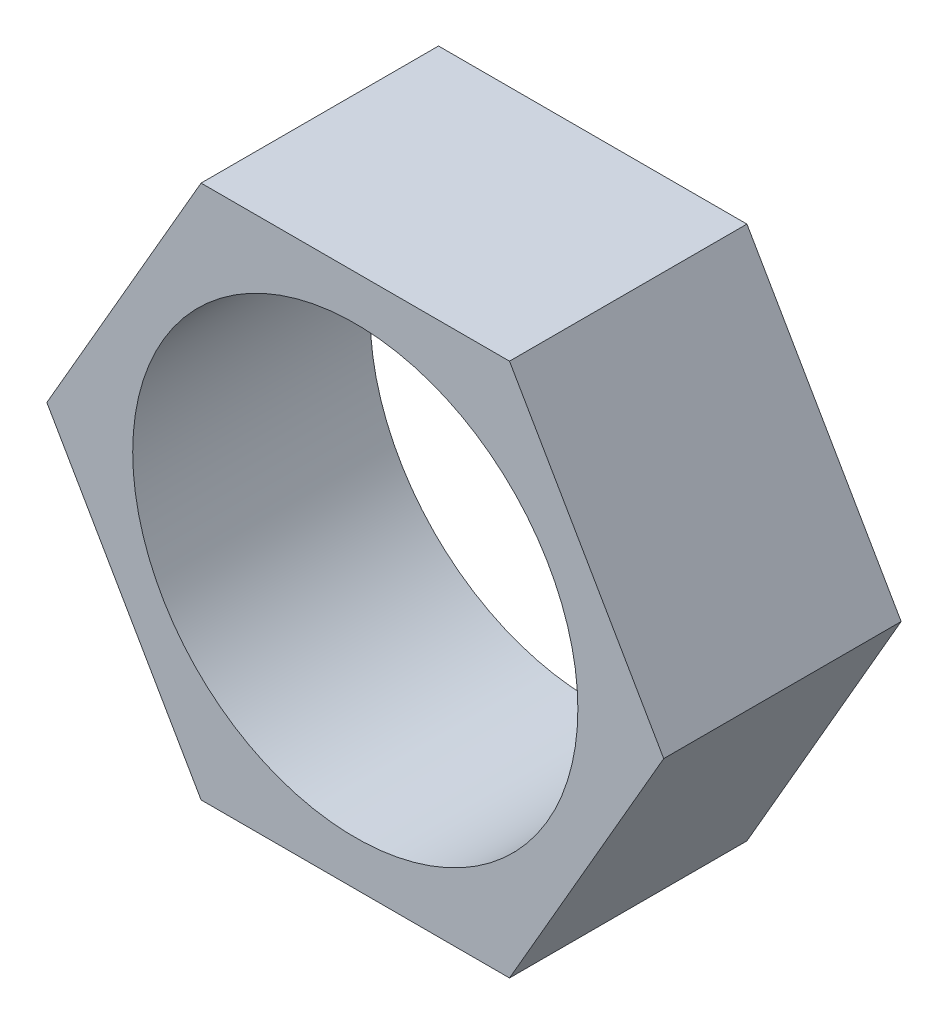
SolidWorks part; units mm, degrees
ref_plane "Ön Düzlem" through (0, 0, 0) normal (0, 0, 1) x (1, 0, 0)
ref_plane "Üst Düzlem" through (0, 0, 0) normal (0, 1, 0) x (1, 0, 0)
ref_plane "Sağ Düzlem" through (0, 0, 0) normal (1, 0, 0) x (0, 0, -1)
sketch "Çizim1" plane through (0, 0, 0) normal (0, 0, 1) x (1, 0, 0)
  line L1 (103.923, 0) -> (51.9615, 90)
  line L2 (51.9615, 90) -> (-51.9615, 90)
  line L3 (-51.9615, 90) -> (-103.923, 0)
  line L4 (-103.923, 0) -> (-51.9615, -90)
  line L5 (-51.9615, -90) -> (51.9615, -90)
  line L6 (51.9615, -90) -> (103.923, 0)
  circle A0 centre (0, 0) radius 90 construction
extrude "Yükseklik-Ekstrüzyon1" add sketch "Çizim1" along normal blind 80
sketch "Çizim3" plane through (0, 0, 0) normal (0, 0, -1) x (-1, 0, 0)
  circle A0 centre (0, 0) radius 75
extrude "Kes-Ekstrüzyon1" cut sketch "Çizim3" against normal blind 134
